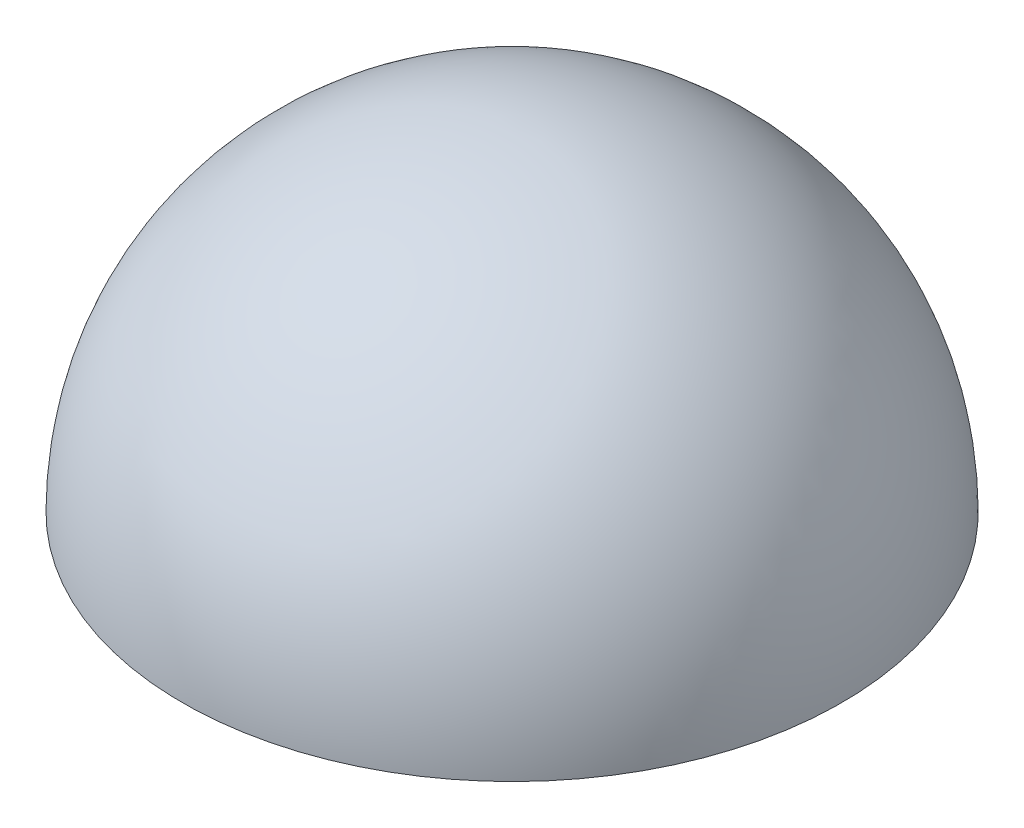
SolidWorks part; units mm, degrees
ref_plane "Front Plane" through (0, 0, 0) normal (0, 0, 1) x (1, 0, 0)
ref_plane "Top Plane" through (0, 0, 0) normal (0, 1, 0) x (1, 0, 0)
ref_plane "Right Plane" through (0, 0, 0) normal (1, 0, 0) x (0, 0, -1)
sketch "Sketch1" plane through (0, 0, 0) normal (0, 1, 0) x (1, 0, 0)
  line L0 (-31.5, 0) -> (31.5, 0) construction
  circle A0 centre (0, 0) radius 30
  circle A1 centre (0, 0) radius 31.5
  dimension "D1" = 60
  dimension "D2" = 1.5
revolve "Revolve2" add sketch "Sketch1" angle 180 about L0
